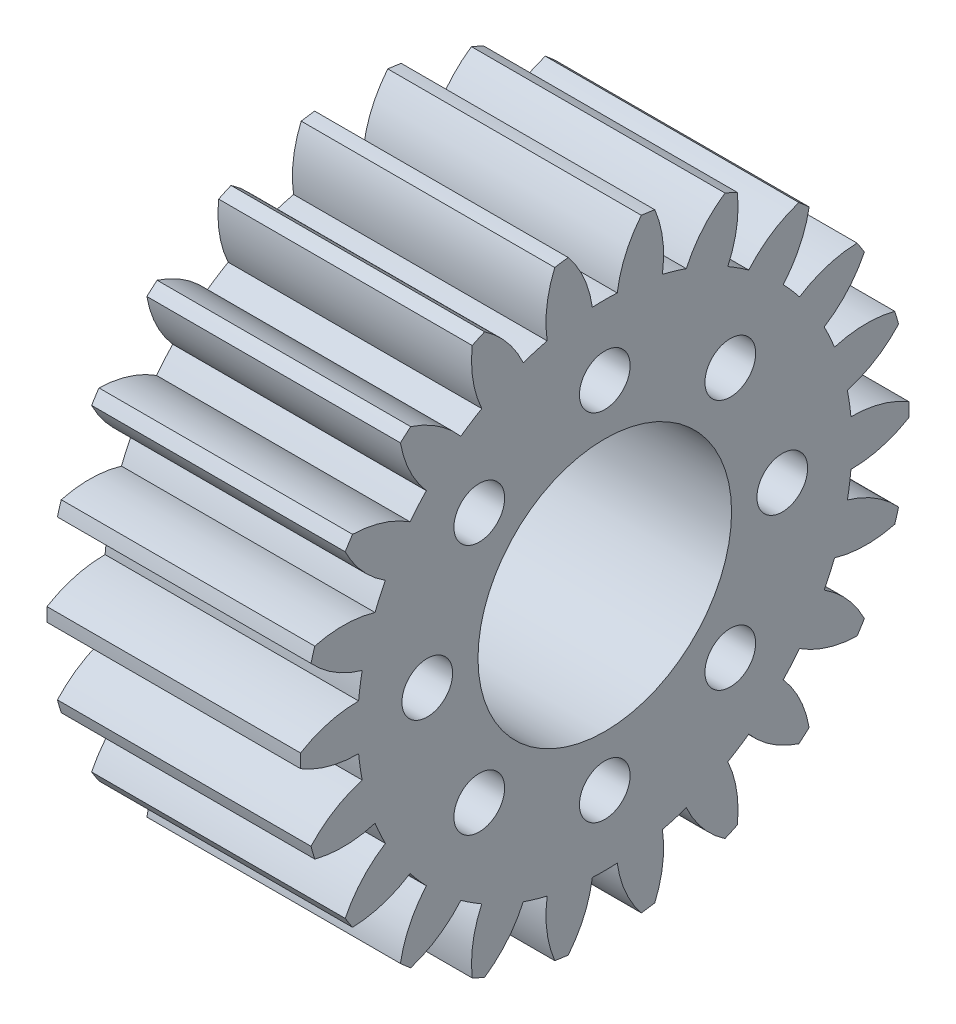
SolidWorks part; units mm, degrees
ref_plane "Plane1" through (0, 0, 0) normal (0, 0, 1) x (1, 0, 0)
ref_plane "Plane2" through (0, 0, 0) normal (0, 1, 0) x (1, 0, 0)
ref_plane "Plane3" through (0, 0, 0) normal (1, 0, 0) x (0, 0, -1)
sketch "HoldingSke" plane through (0, 0, 0) normal (0, 1, 0) x (1, 0, 0)
  line L0 (0, 0) -> (0.9272, -0.3746)
  line L1 (-15, 0) -> (100, 0) construction
  line L2 (0, 0) -> (-2.1039, 2.3779)
  line L3 (0, 0) -> (-11.863, 4.5341)
  line L4 (0, 0) -> (8.0072, 3.2351)
  line L5 (0, 0) -> (-46.8476, -17.4728)
  line L6 (0, 0) -> (-8.2896, -5.593)
  line L7 (-2.1039, 2.3779) -> (8.6586, 51.2059)
  line L8 (-76.2, 54.61) -> (-74.4, 54.61)
  line L9 (-71.009, 38.7566) -> (-53.1078, 45.2721)
  line L10 (-76.2, 71.12) -> (104.1128, 71.12)
  line L11 (0, 0) -> (-10, 0)
  line L12 (-76.2, 101.6) -> (-76.162, 101.6)
  line L13 (24.9733, 27.94) -> (52.9518, 28.4284)
  line L14 (24.9733, 27.94) -> (24.9743, 27.94)
  line L15 (24.9733, 27.94) -> (100.4006, 29.5858)
  line L16 (-63.627, -1) -> (-12.827, -1)
  circle A0 centre (0, 0) radius 5
  circle A1 centre (0, 0) radius 9.749
  circle A2 centre (0, 0) radius 37.5
  circle A3 centre (0, 0) radius 5
  dimension "MHD" = 19.498
  dimension "Hub_dia" = 75
  dimension "Bore" = 10
  dimension "MBD" = 10
  dimension "Num_teeth" = 22
  dimension "Pitch" = 1
  dimension "Overall_len" = 50
  dimension "Show_teeth" = 22
  dimension "Thickness" = 10
  dimension "OAL" = 50.0001
  dimension "T_dim" = 1.8
  dimension "Ap" = 20
  dimension "H" = 19.05
  dimension "Pitch_radius" = 180.3128
  dimension "Width" = 10
  dimension "Backlash" = 0.038
  dimension "Addendum_fac" = 1
  dimension "Dedendum_fac" = 1.25
  dimension "Clearance_fac" = 0.25
  dimension "Dedendum_add" = 0.001
  dimension "Module" = 1
sketch "BasProSke" plane through (0, 0, 0) normal (0, 1, 0) x (1, 0, 0)
  line L0 (-10, 0) -> (60, 0) construction
  line L1 (0, 0) -> (0, 12)
  line L2 (0, 0) -> (10, 0)
  line L3 (10, 0) -> (10, 12)
  line L4 (10, 12) -> (0, 12)
  dimension "Thickness" = 10
  dimension "Diameter" = 24
revolve "Base-Revolve" add sketch "BasProSke" angle 360 about L0
sketch "TooCutSke" plane through (0, 0, 0) normal (1, 0, 0) x (0, 0, -1)
  line L1 (0, 0) -> (0, 107) construction
  line L2 (0, 0) -> (-0.8512, 10.967) construction
  line L3 (0, 0) -> (-3.1242, 21.7296) construction
  line L4 (-0.8512, 10.967) -> (-1.5621, 10.8648) construction
  arc A0 (0.491, 9.7366) -> (-0.491, 9.7366) centre (0, 0) ccw
  arc A1 (1.4609, 11.9363) -> (-1.4609, 11.9363) centre (0, 0) ccw
  circle A2 centre (0, 0) radius 11 construction
  circle A3 centre (0, 0) radius 10.3366 construction
  arc A4 (-0.491, 9.7366) -> (-1.4609, 11.9363) centre (-4.8488, 9.1288) ccw
  arc A5 (1.4609, 11.9363) -> (0.491, 9.7366) centre (4.8488, 9.1288) ccw
  dimension "Root_dia" = 19.498
  dimension "Overcut_dia" = 24.0508
  dimension "Pitch_dia" = 22
  dimension "Base_dia" = 20.6732
  dimension "Flank_rad" = 4.4
  dimension "Half_ang" = 8.182
  dimension "Half_CT" = 0.7182
extrude "ToothCut" cut sketch "TooCutSke" along normal through all
fillet "Breaks" [suppressed] radius 0.02
fillet "RootFillets" [suppressed] radius 0.251
pattern_circular "TeethCuts" count 22 every 16.364 about axis through (-10, 0, 0) along (1, 0, 0) of "ToothCut", "RootFillets", "Breaks"
sketch "HubNeaOneSke" plane through (0, 0, 0) normal (-1, 0, 0) x (0, 0, 1)
  circle A0 centre (0, 0) radius 9.749
  dimension "Diameter" = 19.498
extrude "HubNearOne" [suppressed] add sketch "HubNeaOneSke" along normal blind 40.0001
sketch "HubNeaBotSke" plane through (0, 0, 0) normal (-1, 0, 0) x (0, 0, 1)
  circle A0 centre (0, 0) radius 9.749
  dimension "Diameter" = 19.498
extrude "HubNearBoth" [suppressed] add sketch "HubNeaBotSke" along normal blind 20
ref_plane "FarPln" through (10, 0, 0) normal (1, 0, 0) x (0, 0, -1)
sketch "HubFarSke" plane through (10, 0, 0) normal (1, 0, 0) x (0, 0, -1)
  circle A0 centre (0, 0) radius 9.749
  dimension "Diameter" = 19.498
extrude "HubFar" [suppressed] add sketch "HubFarSke" along normal blind 20
sketch "BorSke" plane through (0, 0, 0) normal (1, 0, 0) x (0, 0, -1)
  circle A0 centre (0, 0) radius 5
  dimension "Diameter" = 10
extrude "Bore" cut sketch "BorSke" along normal mid plane 100.0001
sketch "KeySke" plane through (0, 0, 0) normal (1, 0, 0) x (0, 0, -1)
  line L0 (-2, 0) -> (-2, 6.8)
  line L1 (-2, 6.8) -> (2, 6.8)
  line L2 (2, 6.8) -> (2, 0)
  line L3 (0, 0) -> (0, 34) construction
  line L4 (-2, 0) -> (2, 0)
  dimension "Offset" = 6.8
  dimension "Width" = 4
extrude "Keyway" [suppressed] cut sketch "KeySke" along normal mid plane 100.0001
pattern_circular "Keyway2" [suppressed] count 2 every 90 about axis through (-10, 0, 0) along (1, 0, 0)
hole_wizard "Dégagement M21" positions "Esquisse1" profile "Esquisse2" hole size "M2" standard "ISO" end condition up to next
sketch "Esquisse1" plane through (10, 0, 0) normal (1, 0, 0) x (0, 0, -1)
  point P0 (0, 7)
  point P8 (4.9497, 4.9497)
  point P9 (7, 0)
  point P10 (4.9497, -4.9497)
  point P11 (0, -7)
  point P12 (-4.9497, -4.9497)
  point P13 (-7, 0)
  point P14 (-4.9497, 4.9497)
  point P15 (0, 0)
  dimension "D1" = 8
sketch "Esquisse2" plane through (10, 7, 0) normal (0, 1, 0) x (0, 0, -1)
  line L0 (0, 0) -> (0, 10)
  line L1 (0, 10) -> (1, 10)
  line L2 (1, 10) -> (1, 0)
  line L5 (1, 0) -> (0, 0)
  line L11 (0, -6.35) -> (0, 107.95) construction
  dimension "Diamètre du perçage jusqu'au prochain" = 2
  dimension "Profondeur du perçage jusqu'au prochain" = 10
equation "' \"Module@HoldingSke\" = 6.35"
equation "' \"Num_teeth@HoldingSke\" = 12"
equation "' \"Ap@HoldingSke\" =  20"
equation "' \"Ap@HoldingSke\" = 20"
equation "' \"Width@HoldingSke\" = 0.5 * 25.4"
equation "' \"Hub_dia@HoldingSke\"= 1 * 25.4"
equation "' \"Hub_dia@HoldingSke\" = 1 * 25.4"
equation "' \"Overall_len@HoldingSke\" = 1.0 * 25.4"
equation "' \"Bore@HoldingSke\" = 0.75 * 25.4"
equation "' \"T_dim@HoldingSke\" = 0.1 * 25.4"
equation "' \"Width@KeySke\" = 0.25 * 25.4"
equation "' \"Show_teeth@HoldingSke\" = 13"
equation "' \"Backlash@HoldingSke\" = 0.009 * 25.4"
equation "' \"Addendum_fac@HoldingSke\" = 1.0"
equation "' \"Dedendum_fac@HoldingSke\" = 1.25"
equation "' \"Dedendum_add@HoldingSke\" = 0.00005 * 25.4"
equation "' \"Clearance_fac@HoldingSke\" = 0.25"
equation "\"Pitch@HoldingSke\" = 1 / \"Module@HoldingSke\""
equation "\"Overcut_dia@TooCutSke\" = (\"Num_teeth@HoldingSke\" + 2 * \"Addendum_fac@HoldingSke\") / \"Pitch@HoldingSke\" + 0.002 * 25.4"
equation "\"Pitch_dia@TooCutSke\" = \"Num_teeth@HoldingSke\" / \"Pitch@HoldingSke\""
equation "\"Base_dia@TooCutSke\" = \"Num_teeth@HoldingSke\" / \"Pitch@HoldingSke\" * cos((\"Ap@HoldingSke\"  * 3.14159265 / 180))"
equation "\"Root_dia@TooCutSke\" = (\"Num_teeth@HoldingSke\" + 2) / \"Pitch@HoldingSke\" - 2 * (\"Addendum_fac@HoldingSke\" + \"Dedendum_fac@HoldingSke\") / \"Pitch@HoldingSke\" - \"Dedendum_add@HoldingSke\" * 2"
equation "\"Half_ang@TooCutSke\" = 180 / \"Num_teeth@HoldingSke\""
equation "\"Half_CT@TooCutSke\" = \"Num_teeth@HoldingSke\" / \"Pitch@HoldingSke\" * sin((3.14159265 / 2 / \"Num_teeth@HoldingSke\")) / 2 - 7 * \"Backlash@HoldingSke\" / 4"
equation "\"Flank_rad@TooCutSke\" = \"Num_teeth@HoldingSke\" / \"Pitch@HoldingSke\" / 5"
equation "\"Radius@RootFillets\" = \"Clearance_fac@HoldingSke\" / \"Pitch@HoldingSke\" + \"Dedendum_add@HoldingSke\""
equation "\"Break_rad@Breaks\" = 0.02 / \"Pitch@HoldingSke\""
equation "\"Thickness@HoldingSke\" = \"Width@HoldingSke\""
equation "\"OAL@HoldingSke\" = \"Thickness@HoldingSke\""
equation "\"MHD@HoldingSke\" = (\"Num_teeth@HoldingSke\" + 2) / \"Pitch@HoldingSke\" - 2 * (\"Addendum_fac@HoldingSke\" + \"Dedendum_fac@HoldingSke\")  / \"Pitch@HoldingSke\" - \"Dedendum_add@HoldingSke\" * 2"
equation "\"MBD@HoldingSke\" = (\"Num_teeth@HoldingSke\" + 2) / \"Pitch@HoldingSke\" - 2 * (\"Addendum_fac@HoldingSke\" + \"Dedendum_fac@HoldingSke\")  / \"Pitch@HoldingSke\" - \"Dedendum_add@HoldingSke\" * 2 - 0.002 * 25.4"
equation "\"MHD@HoldingSke\" = ((sgn( \"MHD@HoldingSke\" - \"Hub_dia@HoldingSke\" )-1)*( \"MHD@HoldingSke\" - \"Hub_dia@HoldingSke\" ))/-2+ \"Hub_dia@HoldingSke\""
equation "\"MBD@HoldingSke\" = ((sgn( \"MBD@HoldingSke\" - \"Bore@HoldingSke\" )-1)*( \"MBD@HoldingSke\" - \"Bore@HoldingSke\" ))/-2+ \"Bore@HoldingSke\""
equation "\"OAL@HoldingSke\" = ((sgn( \"OAL@HoldingSke\" - \"Overall_len@HoldingSke\" )+1)*( \"OAL@HoldingSke\" - \"Overall_len@HoldingSke\" ))/2 + \"Overall_len@HoldingSke\" + 0.000002 * 25.4"
equation "\"Num_teeth@TeethCuts\" = int( \"Show_teeth@HoldingSke\" ) + 1"
equation "\"Num_teeth@TeethCuts\" = ((sgn( \"Num_teeth@TeethCuts\" - \"Num_teeth@HoldingSke\" )-1)*( \"Num_teeth@TeethCuts\" - \"Num_teeth@HoldingSke\" ))/-2+ \"Num_teeth@HoldingSke\""
equation "\"Num_teeth@TeethCuts\" = ((sgn( \"Num_teeth@TeethCuts\" - 2.0)+1)*( \"Num_teeth@TeethCuts\" - 2.0))/2 +2.0"
equation "\"Angle@TeethCuts\" = 360.0 / \"Num_teeth@HoldingSke\""
equation "\"Diameter@BasProSke\" = (\"Num_teeth@HoldingSke\" + 2 * \"Addendum_fac@HoldingSke\") / \"Pitch@HoldingSke\""
equation "\"Thickness@BasProSke\"  = \"Thickness@HoldingSke\""
equation "' \"Fillet_rad@BasProSke\" =  \"Thickness@HoldingSke\" * 0.05"
equation "' \"Fillet_rad@BasProSke\" = \"Thickness@HoldingSke\" * 0.05"
equation "\"MHD@HoldingSke\" = ((sgn( \"MHD@HoldingSke\" - \"Root_dia@TooCutSke\" )-1)*( \"MHD@HoldingSke\" - \"Root_dia@TooCutSke\" ))/-2+ \"Root_dia@TooCutSke\""
equation "\"Diameter@HubNeaOneSke\" = \"MHD@HoldingSke\""
equation "\"Length@HubNearOne\" = \"OAL@HoldingSke\" - \"Thickness@BasProSke\""
equation "\"Diameter@HubNeaBotSke\" = \"MHD@HoldingSke\""
equation "\"Length@HubNearBoth\" = ( \"OAL@HoldingSke\" - \"Thickness@BasProSke\" ) / 2.0"
equation "\"Thickness@FarPln\" = \"Thickness@BasProSke\""
equation "\"Diameter@HubFarSke\" = \"MHD@HoldingSke\""
equation "\"Length@HubFar\" = ( \"OAL@HoldingSke\" - \"Thickness@BasProSke\" ) / 2.0"
equation "\"Diameter@BorSke\" = \"MBD@HoldingSke\""
equation "\"D1@Bore\" = \"OAL@HoldingSke\" * 2.0"
equation "\"D1@Keyway\" = \"OAL@HoldingSke\" * 2.0"
equation "\"Offset@KeySke\" = \"T_dim@HoldingSke\" + \"MBD@HoldingSke\" / 2.0"
